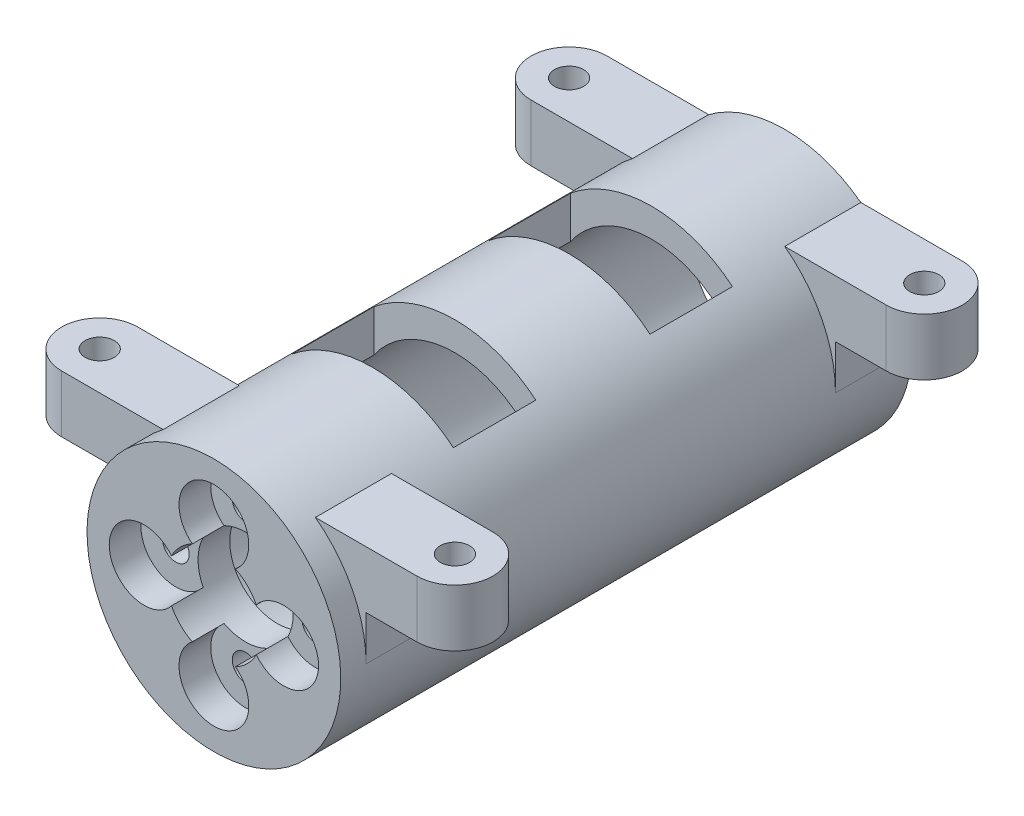
SolidWorks part; units mm, degrees
ref_plane "Ebene vorne" through (0, 0, 0) normal (0, 0, 1) x (1, 0, 0)
ref_plane "Ebene oben" through (0, 0, 0) normal (0, 1, 0) x (1, 0, 0)
ref_plane "Ebene rechts" through (0, 0, 0) normal (1, 0, 0) x (0, 0, -1)
sketch "Skizze5" plane through (0, 0, 0) normal (1, 0, 0) x (0, 0, -1)
  line L0 (40, 7.75) -> (0, 7.75)
  line L1 (0, 7.75) -> (0, 3.75)
  line L2 (0, 3.75) -> (-1, 3.75)
  line L3 (-1, 3.75) -> (-1, 3.25)
  line L4 (-1, 3.25) -> (-2.6, 3.25)
  line L5 (-2.6, 3.25) -> (-2.6, 2)
  line L6 (-2.6, 2) -> (-5, 2)
  line L7 (-5, 2) -> (-5, 10)
  line L8 (-5, 10) -> (40, 10)
  line L9 (40, 10) -> (40, 7.75)
  line L10 (0, 0) -> (-14.2607, 0) construction
  line L11 (-2.6, 1.5) -> (-12.3, 1.5) construction
  line L12 (-1, 3) -> (-2.6, 3) construction
  line L13 (0, 3.5) -> (-1, 3.5) construction
  line L14 (0, 7.5) -> (0, -7.5) construction
  line L15 (-1, 3.5) -> (-1, -3.5) construction
  line L16 (-2.6, 3) -> (-2.6, -3) construction
  line L17 (11.7, 7.5) -> (0, 7.5) construction
  dimension "D1" = 5
  dimension "D2" = 0.5
  dimension "D3" = 0.25
  dimension "D4" = 0.25
  dimension "D5" = 0.25
  dimension "D6" = 2.25
  dimension "D7" = 45
revolve "Rotation1" add sketch "Skizze5" angle 360 about L10
sketch "Skizze6" plane through (0, 0, 5) normal (0, 0, 1) x (1, 0, 0)
  line L0 (0, 0) -> (5.5, 0) construction
  line L1 (2.8916, 2.8916) -> (5.6259, 5.6259) construction
  line L2 (0, 0) -> (0, 4.45) construction
  line L3 (0, 0) -> (4.45, 0) construction
  circle A0 centre (0, 5.5) radius 1.05
  circle A1 centre (0, 5.5) radius 0.8 construction
  circle A2 centre (0, -5.5) radius 1.05
  circle A3 centre (5.5, 0) radius 1.05
  circle A4 centre (-5.5, 0) radius 1.05
  point P17 (0.4102, -0.3826)
  dimension "D1" = 0.25
extrude "Schnitt-Linear austragen3" cut sketch "Skizze6" against normal through all
sketch "Skizze7" plane through (0, 0, 5) normal (0, 0, 1) x (1, 0, 0)
  line L0 (0, 0) -> (3.4364, 0) construction
  line L1 (0, 1.0151) -> (0, 0) construction
  line L2 (0, 0) -> (4.7563, 4.7563) construction
  circle A0 centre (0, 5.5) radius 2.75
  circle A1 centre (0, -5.5) radius 2.75
  circle A2 centre (5.5, 0) radius 2.75
  circle A3 centre (-5.5, 0) radius 2.75
  point P15 (-5.5, 0)
  point P17 (5.5, 0)
  dimension "D1" = 5.5
extrude "Schnitt-Linear austragen4" cut sketch "Skizze7" against normal blind 2.5
ref_plane "Ebene1" through (0, 10, 0) normal (0, 1, 0) x (1, 0, 0)
sketch "Skizze12" plane through (0, 0, 5) normal (0, 0, 1) x (1, 0, 0)
  line L0 (-10, 0) -> (-10, 8)
  line L1 (-10, 8) -> (-6, 8)
  line L2 (-10, 0) -> (0, 0) construction
  line L3 (-8.1954, 10) -> (7.5336, 10) construction
  line L4 (0, 0) -> (0, 3.2281) construction
  line L5 (10, 8) -> (6, 8)
  line L6 (10, 0) -> (10, 8)
  arc A0 (-10, 0) -> (-6, 8) centre (0, 0) cw
  circle A1 centre (0, 0) radius 10 construction
  arc A2 (10, 0) -> (6, 8) centre (0, 0) ccw
  dimension "D1" = 2
extrude "Aufsatz-Linear austragen6" add sketch "Skizze12" against normal blind 6 from offset 2 offset against normal yes
ref_plane "Ebene2" through (0, 0, -18.5) normal (0, 0, -1) x (-1, 0, 0)
mirror "Spiegeln1" about plane through (0, 0, -18.5) normal (0, 0, -1) of "Aufsatz-Linear austragen6"
sketch "Skizze13" plane through (0, 8, 0) normal (0, 1, 0) x (1, 0, 0)
  line L0 (-14, 40) -> (-10, 40)
  line L1 (-10, 40) -> (-10, 34)
  line L2 (-20.4759, 37) -> (-10, 37) construction
  line L3 (-14, 34) -> (-10, 34)
  line L4 (0, 25.2988) -> (0, 18.5) construction
  line L5 (0, 18.5) -> (13.2902, 18.5) construction
  line L6 (20.4759, 37) -> (10, 37) construction
  line L7 (14, 34) -> (10, 34)
  line L8 (10, 40) -> (10, 34)
  line L9 (14, 40) -> (10, 40)
  line L10 (20.4759, 0) -> (10, 0) construction
  line L11 (0, 11.7012) -> (0, 18.5) construction
  line L12 (-20.4759, 0) -> (-10, 0) construction
  line L13 (14, -3) -> (10, -3)
  line L14 (10, -3) -> (10, 3)
  line L15 (14, 3) -> (10, 3)
  line L16 (-14, 3) -> (-10, 3)
  line L17 (-10, -3) -> (-10, 3)
  line L18 (-14, -3) -> (-10, -3)
  line L21 (-10, 34) -> (-10, 40) construction
  line L22 (-6, 34) -> (-10, 34) construction
  line L23 (10, -3) -> (6, -3) construction
  line L24 (10, 3) -> (10, -3) construction
  arc A0 (-14, 40) -> (-14, 34) centre (-14, 37) ccw
  arc A1 (14, 40) -> (14, 34) centre (14, 37) cw
  arc A2 (14, -3) -> (14, 3) centre (14, 0) ccw
  arc A3 (-14, -3) -> (-14, 3) centre (-14, 0) cw
  dimension "D1" = 4
extrude "Aufsatz-Linear austragen7" add sketch "Skizze13" against normal blind 4.5
sketch "Skizze14" plane through (0, 3.5, 0) normal (0, -1, 0) x (-1, 0, 0)
  line L0 (0, -8.5703) -> (0, 18.5) construction
  line L1 (0, 18.5) -> (-24.3743, 18.5) construction
  circle A0 centre (14, 0) radius 1.15
  circle A1 centre (-14, 0) radius 1.15
  circle A2 centre (-14, 37) radius 1.15
  circle A3 centre (14, 37) radius 1.15
  arc A4 (-14, 40) -> (-14, 34) centre (-14, 37) ccw construction
  dimension "D1" = 2.3
extrude "Schnitt-Linear austragen5" cut sketch "Skizze14" against normal through all
sketch "Skizze17" plane through (0, 0, 0) normal (1, 0, 0) x (0, 0, -1)
  line L1 (7.5, 10.1) -> (14, 10.1)
  line L2 (7.5, 10.1) -> (7.5, 7.7)
  line L3 (7.5, 7.7) -> (14, 7.7)
  line L4 (14, 10.1) -> (14, 7.7)
  line L5 (3, 8) -> (34, 8) construction
  line L6 (18.5, 8) -> (18.5, -10) construction
  line L7 (-5, -10) -> (40, -10) construction
  line L8 (23, 10.1) -> (23, 7.7)
  line L9 (29.5, 7.7) -> (23, 7.7)
  line L10 (29.5, 10.1) -> (29.5, 7.7)
  line L11 (29.5, 10.1) -> (23, 10.1)
  line L12 (10.75, 7.7) -> (10.75, 10.1) construction
  line L13 (3, 6.4214) -> (18.5, 6.4214) construction
  line L14 (3, 0) -> (3, 8) construction
  line L15 (40, 10) -> (-5, 10) construction
  point P25 (10.75, 6.4214)
  dimension "D1" = 6.5
  dimension "D2" = 0.3
  dimension "D3" = 0.1
extrude "Schnitt-Linear austragen9" cut sketch "Skizze17" against normal through all and the other way through all
sketch "Skizze18" plane through (0, 7.7, 0) normal (0, 1, 0) x (1, 0, 0)
  line L1 (-6.3804, 14) -> (6.3804, 14)
  line L2 (-6.3804, 14) -> (-6.3804, 7.5)
  line L3 (-6.3804, 7.5) -> (6.3804, 7.5)
  line L4 (6.3804, 14) -> (6.3804, 7.5)
  line L5 (-6.3804, 29.5) -> (6.3804, 29.5)
  line L6 (-6.3804, 29.5) -> (-6.3804, 23)
  line L7 (-6.3804, 23) -> (6.3804, 23)
  line L8 (6.3804, 29.5) -> (6.3804, 23)
extrude "Schnitt-Linear austragen10" cut sketch "Skizze18" against normal up to surface (12.0991 mm away)
sketch "Skizze19" plane through (0, 0, 0) normal (0, 0, -1) x (-1, 0, 0)
  circle A0 centre (0, 0) radius 3.75
  circle A1 centre (0, 0) radius 3.75 construction
extrude "Schnitt-Linear austragen11" cut sketch "Skizze19" against normal through all
equation "\"M2EinschmelzGewindeDurchmesser\"= 3.4"
equation "\"M2EinschmelzGewindeTiefe\"= 4"
equation "\"M3EinschmelzGewindeDurchmesser\"= 4.2"
equation "\"M3EinschmelzGewindeTief\"= 5.7"
equation "\"M2SchraubeLoch\"=2.3"
equation "\"D1@Skizze14\"=\"M2SchraubeLoch\""
